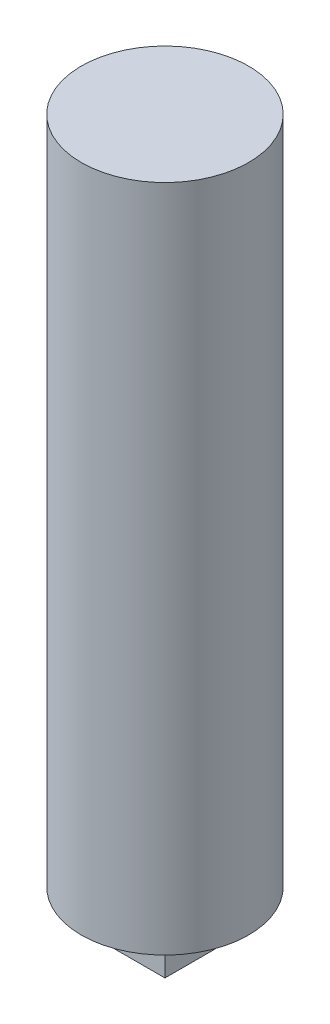
SolidWorks part; units mm, degrees
ref_plane "Front Plane" through (0, 0, 0) normal (0, 0, 1) x (1, 0, 0)
ref_plane "Top Plane" through (0, 0, 0) normal (0, 1, 0) x (1, 0, 0)
ref_plane "Right Plane" through (0, 0, 0) normal (1, 0, 0) x (0, 0, -1)
sketch "Sketch1" plane through (0, 0, 0) normal (0, 1, 0) x (1, 0, 0)
  circle A0 centre (0, 0) radius 6.25
  dimension "D1" = 12.5
extrude "Boss-Extrude1" add sketch "Sketch1" along normal blind 50
sketch "Sketch2" plane through (0, 0, 0) normal (0, -1, 0) x (1, 0, 0)
  circle A0 centre (0, 0) radius 4.5
  dimension "D1" = 9
extrude "Cut-Extrude1" cut sketch "Sketch2" against normal blind 1
sketch "Sketch3" plane through (0, 1, 0) normal (0, -1, 0) x (-1, 0, 0)
  line L1 (-1.9, -1.9) -> (1.9, -1.9)
  line L2 (-1.9, -1.9) -> (-1.9, 1.9)
  line L3 (-1.9, 1.9) -> (1.9, 1.9)
  line L4 (1.9, -1.9) -> (1.9, 1.9)
  dimension "D1" = 3.8
  dimension "D2" = 3.8
  dimension "D3" = 1.9
  dimension "D4" = 1.9
extrude "Boss-Extrude2" add sketch "Sketch3" along normal blind 5
